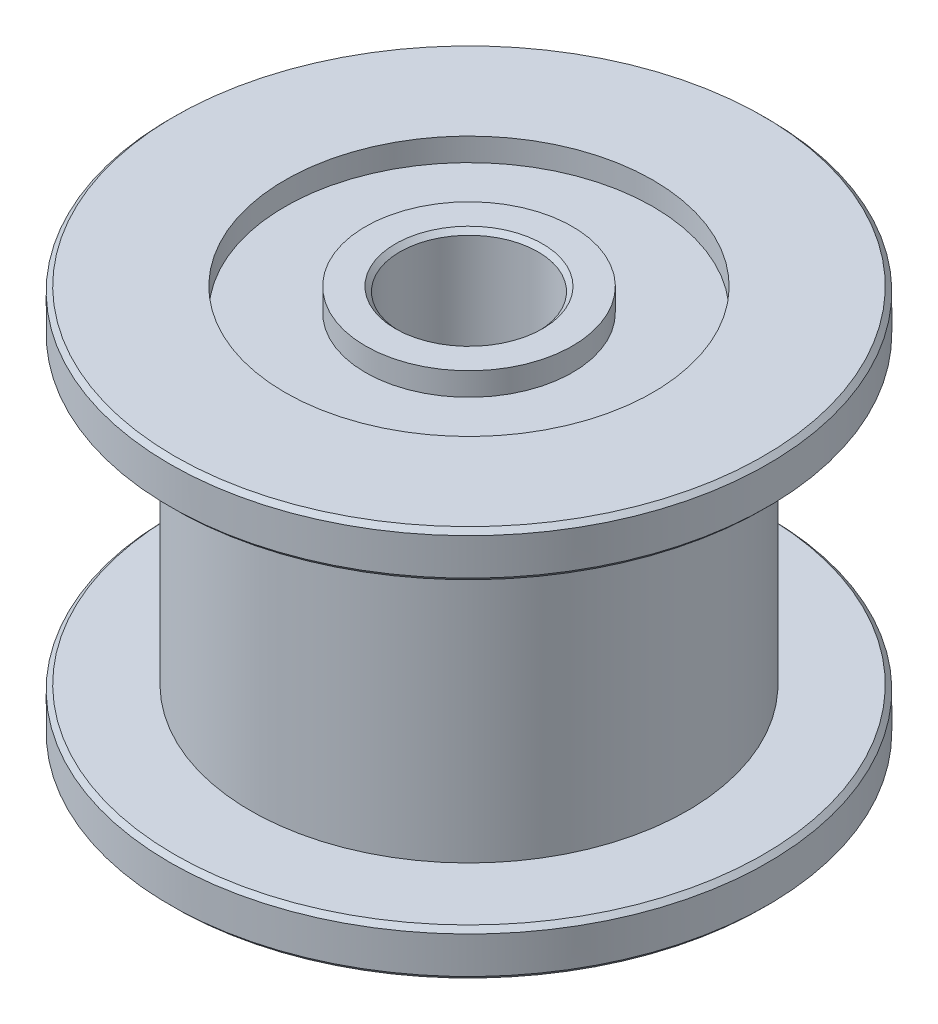
SolidWorks part; units mm, degrees
ref_plane "Front Plane" through (0, 0, 0) normal (0, 0, 1) x (1, 0, 0)
ref_plane "Top Plane" through (0, 0, 0) normal (0, 1, 0) x (1, 0, 0)
ref_plane "Right Plane" through (0, 0, 0) normal (1, 0, 0) x (0, 0, -1)
sketch "Sketch1" plane through (0, 0, 0) normal (1, 0, 0) x (0, 0, -1)
  line L0 (1.5, -4.25) -> (1.5, 4.25)
  line L1 (1.5, 4.25) -> (6.5, 4.25)
  line L2 (6.5, 4.25) -> (6.5, 3.25)
  line L3 (6.5, 3.25) -> (4.75, 3.25)
  line L4 (4.75, 3.25) -> (4.75, -3.25)
  line L5 (4.75, -3.25) -> (6.5, -3.25)
  line L6 (6.5, -3.25) -> (6.5, -4.25)
  line L7 (6.5, -4.25) -> (1.5, -4.25)
  line L8 (0, 0) -> (0, 9.3746) construction
  point P11 (1.5, 0)
  dimension "D1" = 1
  dimension "D2" = 8.5
  dimension "D3" = 13
  dimension "D4" = 9.5
  dimension "D5" = 3
  dimension "D6" = 6.5
revolve "Revolve1" add sketch "Sketch1" angle 360 about L8
chamfer "Chamfer1" distance 0.1 angle 45 6 edges at (0, 4.25, -1.5) (0, -4.25, -1.5) (0, -4.25, -6.5) (0, -3.25, -6.5) (0, 3.25, -6.5) (0, 4.25, -6.5)
sketch "Sketch2" plane through (0, 4.25, 0) normal (0, 1, 0) x (1, 0, 0)
  circle A0 centre (0, 0) radius 4
  circle A1 centre (0, 0) radius 2.25
  dimension "D1" = 8
  dimension "D2" = 4.5
extrude "Cut-Extrude1" cut sketch "Sketch2" against normal blind 0.5
mirror "Mirror1" about plane through (0, 0, 0) normal (0, 1, 0) of "Cut-Extrude1"
